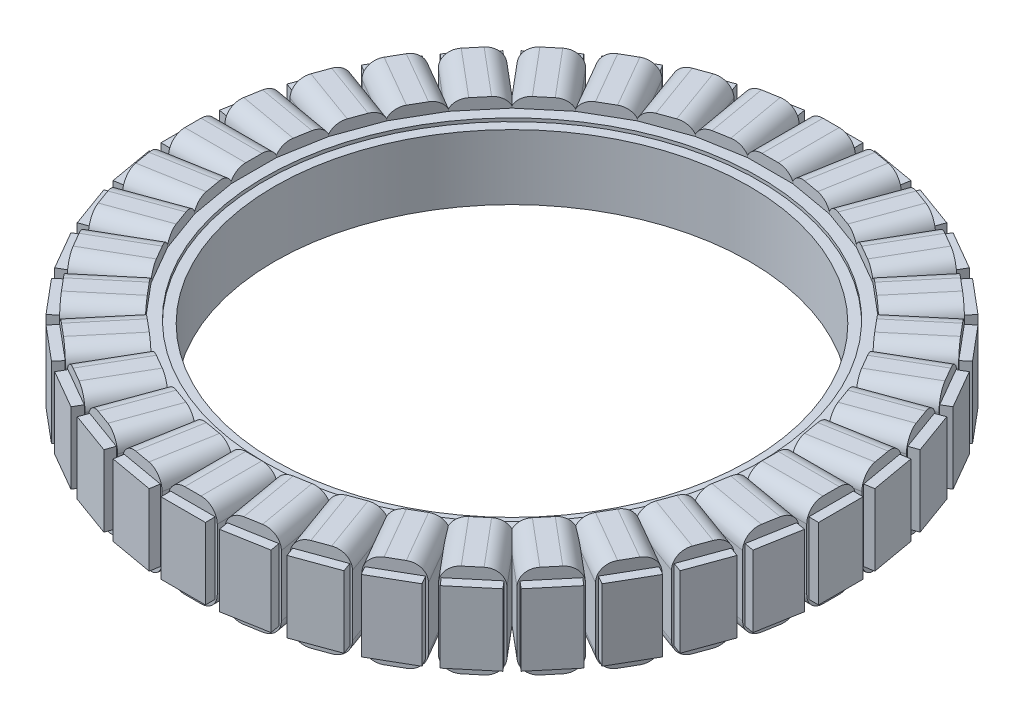
SolidWorks part; units mm, degrees
ref_plane "Front Plane" through (0, 0, 0) normal (0, 0, 1) x (1, 0, 0)
ref_plane "Top Plane" through (0, 0, 0) normal (0, 1, 0) x (1, 0, 0)
ref_plane "Right Plane" through (0, 0, 0) normal (1, 0, 0) x (0, 0, -1)
sketch "Sketch1" plane through (0, 0, 0) normal (0, 1, 0) x (1, 0, 0)
  circle A0 centre (0, 0) radius 29.25
  circle A1 centre (0, 0) radius 30.45
  dimension "D1" = 58.5
  dimension "D2" = 1.2
extrude "Boss-Extrude1" add sketch "Sketch1" along normal mid plane 8
sketch "Sketch2" plane through (0, 0, 0) normal (0, 1, 0) x (1, 0, 0)
  line L0 (0, 0) -> (0, 40.5) construction
  line L1 (-3.5433, 40.5) -> (-10.5222, 39.2694)
  line L2 (-10.5222, 39.2694) -> (-17.1814, 36.8457)
  line L3 (-17.1814, 36.8457) -> (-23.3186, 33.3024)
  line L4 (-23.3186, 33.3024) -> (-28.7472, 28.7472)
  line L5 (-28.7472, 28.7472) -> (-33.3024, 23.3186)
  line L6 (-33.3024, 23.3186) -> (-36.8457, 17.1814)
  line L7 (-36.8457, 17.1814) -> (-39.2694, 10.5222)
  line L8 (-39.2694, 10.5222) -> (-40.5, 3.5433)
  line L9 (-40.5, 3.5433) -> (-40.5, -3.5433)
  line L10 (-40.5, -3.5433) -> (-39.2694, -10.5222)
  line L11 (-39.2694, -10.5222) -> (-36.8457, -17.1814)
  line L12 (-36.8457, -17.1814) -> (-33.3024, -23.3186)
  line L13 (-33.3024, -23.3186) -> (-28.7472, -28.7472)
  line L14 (-28.7472, -28.7472) -> (-23.3186, -33.3024)
  line L15 (-23.3186, -33.3024) -> (-17.1814, -36.8457)
  line L16 (-17.1814, -36.8457) -> (-10.5222, -39.2694)
  line L17 (-10.5222, -39.2694) -> (-3.5433, -40.5)
  line L18 (-3.5433, -40.5) -> (3.5433, -40.5)
  line L19 (3.5433, -40.5) -> (10.5222, -39.2694)
  line L20 (10.5222, -39.2694) -> (17.1814, -36.8457)
  line L21 (17.1814, -36.8457) -> (23.3186, -33.3024)
  line L22 (23.3186, -33.3024) -> (28.7472, -28.7472)
  line L23 (28.7472, -28.7472) -> (33.3024, -23.3186)
  line L24 (33.3024, -23.3186) -> (36.8457, -17.1814)
  line L25 (36.8457, -17.1814) -> (39.2694, -10.5222)
  line L26 (39.2694, -10.5222) -> (40.5, -3.5433)
  line L27 (40.5, -3.5433) -> (40.5, 3.5433)
  line L28 (40.5, 3.5433) -> (39.2694, 10.5222)
  line L29 (39.2694, 10.5222) -> (36.8457, 17.1814)
  line L30 (36.8457, 17.1814) -> (33.3024, 23.3186)
  line L31 (33.3024, 23.3186) -> (28.7472, 28.7472)
  line L32 (28.7472, 28.7472) -> (23.3186, 33.3024)
  line L33 (23.3186, 33.3024) -> (17.1814, 36.8457)
  line L34 (17.1814, 36.8457) -> (10.5222, 39.2694)
  line L35 (10.5222, 39.2694) -> (3.5433, 40.5)
  line L36 (3.5433, 40.5) -> (-3.5433, 40.5)
  circle A1 centre (0, 0) radius 30.45
  circle A2 centre (0, 0) radius 40.5 construction
  circle A3 centre (0, 0) radius 30.45 construction
  dimension "D1" = 81
extrude "Boss-Extrude2" add sketch "Sketch2" along normal mid plane 8.8
sketch "Sketch4" plane through (0, 4.4, 0) normal (0, 1, 0) x (1, 0, 0)
  line L0 (0, 0) -> (0, 40.5) construction
  line L1 (3.5433, 40.5) -> (-3.5433, 40.5) construction
  line L2 (0, 0) -> (3.5433, 40.5) construction
  line L3 (1, 39.3) -> (2.7402, 39.3)
  line L4 (1, 39.3) -> (1, 31.9846)
  line L5 (10.5222, 39.2694) -> (3.5433, 40.5) construction
  line L6 (1, 31.9846) -> (4.5693, 31.6723)
  line L7 (4.5693, 31.6723) -> (5.8396, 38.8766)
  line L8 (2.7402, 39.3) -> (2.7402, 40.5)
  line L9 (2.7402, 40.5) -> (3.5433, 40.5)
  line L10 (3.5433, 40.5) -> (4.3341, 40.3606)
  line L11 (4.3341, 40.3606) -> (4.1258, 39.1788)
  line L12 (4.1258, 39.1788) -> (5.8396, 38.8766)
  line L13 (7.8092, 38.5293) -> (9.523, 38.2271)
  line L14 (7.8092, 38.5293) -> (6.5389, 31.325)
  line L15 (6.5389, 31.325) -> (9.9997, 30.3977)
  line L16 (9.9997, 30.3977) -> (12.5017, 37.2719)
  line L17 (9.523, 38.2271) -> (9.7314, 39.4089)
  line L18 (9.7314, 39.4089) -> (10.5222, 39.2694)
  line L19 (10.5222, 39.2694) -> (11.2768, 38.9948)
  line L20 (11.2768, 38.9948) -> (10.8664, 37.8671)
  line L21 (10.8664, 37.8671) -> (12.5017, 37.2719)
  line L22 (14.3811, 36.5879) -> (16.0164, 35.9927)
  line L23 (14.3811, 36.5879) -> (11.8791, 29.7136)
  line L24 (11.8791, 29.7136) -> (15.1263, 28.1994)
  line L25 (15.1263, 28.1994) -> (18.784, 34.5348)
  line L26 (16.0164, 35.9927) -> (16.4268, 37.1203)
  line L27 (16.4268, 37.1203) -> (17.1814, 36.8457)
  line L28 (17.1814, 36.8457) -> (17.8769, 36.4441)
  line L29 (17.8769, 36.4441) -> (17.2769, 35.4049)
  line L30 (17.2769, 35.4049) -> (18.784, 34.5348)
  line L31 (20.516, 33.5348) -> (22.0231, 32.6647)
  line L32 (20.516, 33.5348) -> (16.8583, 27.1994)
  line L33 (16.8583, 27.1994) -> (19.7932, 25.1444)
  line L34 (19.7932, 25.1444) -> (24.4955, 30.7483)
  line L35 (22.0231, 32.6647) -> (22.6231, 33.7039)
  line L36 (22.6231, 33.7039) -> (23.3186, 33.3024)
  line L37 (23.3186, 33.3024) -> (23.9338, 32.7862)
  line L38 (23.9338, 32.7862) -> (23.1624, 31.8669)
  line L39 (23.1624, 31.8669) -> (24.4955, 30.7483)
  line L40 (26.0276, 29.4628) -> (27.3607, 28.3442)
  line L41 (26.0276, 29.4628) -> (21.3253, 23.8588)
  line L42 (21.3253, 23.8588) -> (23.8588, 21.3253)
  line L43 (23.8588, 21.3253) -> (29.4628, 26.0276)
  line L44 (27.3607, 28.3442) -> (28.132, 29.2634)
  line L45 (28.132, 29.2634) -> (28.7472, 28.7472)
  line L46 (28.7472, 28.7472) -> (29.2634, 28.132)
  line L47 (29.2634, 28.132) -> (28.3442, 27.3607)
  line L48 (28.3442, 27.3607) -> (29.4628, 26.0276)
  line L49 (30.7483, 24.4955) -> (31.8669, 23.1624)
  line L50 (30.7483, 24.4955) -> (25.1444, 19.7932)
  line L51 (25.1444, 19.7932) -> (27.1994, 16.8583)
  line L52 (27.1994, 16.8583) -> (33.5348, 20.516)
  line L53 (31.8669, 23.1624) -> (32.7862, 23.9338)
  line L54 (32.7862, 23.9338) -> (33.3024, 23.3186)
  line L55 (33.3024, 23.3186) -> (33.7039, 22.6231)
  line L56 (33.7039, 22.6231) -> (32.6647, 22.0231)
  line L57 (32.6647, 22.0231) -> (33.5348, 20.516)
  line L58 (34.5348, 18.784) -> (35.4049, 17.2769)
  line L59 (34.5348, 18.784) -> (28.1994, 15.1263)
  line L60 (28.1994, 15.1263) -> (29.7136, 11.8791)
  line L61 (29.7136, 11.8791) -> (36.5879, 14.3811)
  line L62 (35.4049, 17.2769) -> (36.4441, 17.8769)
  line L63 (36.4441, 17.8769) -> (36.8457, 17.1814)
  line L64 (36.8457, 17.1814) -> (37.1203, 16.4268)
  line L65 (37.1203, 16.4268) -> (35.9927, 16.0164)
  line L66 (35.9927, 16.0164) -> (36.5879, 14.3811)
  line L67 (37.2719, 12.5017) -> (37.8671, 10.8664)
  line L68 (37.2719, 12.5017) -> (30.3977, 9.9997)
  line L69 (30.3977, 9.9997) -> (31.325, 6.5389)
  line L70 (31.325, 6.5389) -> (38.5293, 7.8092)
  line L71 (37.8671, 10.8664) -> (38.9948, 11.2768)
  line L72 (38.9948, 11.2768) -> (39.2694, 10.5222)
  line L73 (39.2694, 10.5222) -> (39.4089, 9.7314)
  line L74 (39.4089, 9.7314) -> (38.2271, 9.523)
  line L75 (38.2271, 9.523) -> (38.5293, 7.8092)
  line L76 (38.8766, 5.8396) -> (39.1788, 4.1258)
  line L77 (38.8766, 5.8396) -> (31.6723, 4.5693)
  line L78 (31.6723, 4.5693) -> (31.9846, 1)
  line L79 (31.9846, 1) -> (39.3, 1)
  line L80 (39.1788, 4.1258) -> (40.3606, 4.3341)
  line L81 (40.3606, 4.3341) -> (40.5, 3.5433)
  line L82 (40.5, 3.5433) -> (40.5, 2.7402)
  line L83 (40.5, 2.7402) -> (39.3, 2.7402)
  line L84 (39.3, 2.7402) -> (39.3, 1)
  line L85 (39.3, -1) -> (39.3, -2.7402)
  line L86 (39.3, -1) -> (31.9846, -1)
  line L87 (31.9846, -1) -> (31.6723, -4.5693)
  line L88 (31.6723, -4.5693) -> (38.8766, -5.8396)
  line L89 (39.3, -2.7402) -> (40.5, -2.7402)
  line L90 (40.5, -2.7402) -> (40.5, -3.5433)
  line L91 (40.5, -3.5433) -> (40.3606, -4.3341)
  line L92 (40.3606, -4.3341) -> (39.1788, -4.1258)
  line L93 (39.1788, -4.1258) -> (38.8766, -5.8396)
  line L94 (38.5293, -7.8092) -> (38.2271, -9.523)
  line L95 (38.5293, -7.8092) -> (31.325, -6.5389)
  line L96 (31.325, -6.5389) -> (30.3977, -9.9997)
  line L97 (30.3977, -9.9997) -> (37.2719, -12.5017)
  line L98 (38.2271, -9.523) -> (39.4089, -9.7314)
  line L99 (39.4089, -9.7314) -> (39.2694, -10.5222)
  line L100 (39.2694, -10.5222) -> (38.9948, -11.2768)
  line L101 (38.9948, -11.2768) -> (37.8671, -10.8664)
  line L102 (37.8671, -10.8664) -> (37.2719, -12.5017)
  line L103 (36.5879, -14.3811) -> (35.9927, -16.0164)
  line L104 (36.5879, -14.3811) -> (29.7136, -11.8791)
  line L105 (29.7136, -11.8791) -> (28.1994, -15.1263)
  line L106 (28.1994, -15.1263) -> (34.5348, -18.784)
  line L107 (35.9927, -16.0164) -> (37.1203, -16.4268)
  line L108 (37.1203, -16.4268) -> (36.8457, -17.1814)
  line L109 (36.8457, -17.1814) -> (36.4441, -17.8769)
  line L110 (36.4441, -17.8769) -> (35.4049, -17.2769)
  line L111 (35.4049, -17.2769) -> (34.5348, -18.784)
  line L112 (33.5348, -20.516) -> (32.6647, -22.0231)
  line L113 (33.5348, -20.516) -> (27.1994, -16.8583)
  line L114 (27.1994, -16.8583) -> (25.1444, -19.7932)
  line L115 (25.1444, -19.7932) -> (30.7483, -24.4955)
  line L116 (32.6647, -22.0231) -> (33.7039, -22.6231)
  line L117 (33.7039, -22.6231) -> (33.3024, -23.3186)
  line L118 (33.3024, -23.3186) -> (32.7862, -23.9338)
  line L119 (32.7862, -23.9338) -> (31.8669, -23.1624)
  line L120 (31.8669, -23.1624) -> (30.7483, -24.4955)
  line L121 (29.4628, -26.0276) -> (28.3442, -27.3607)
  line L122 (29.4628, -26.0276) -> (23.8588, -21.3253)
  line L123 (23.8588, -21.3253) -> (21.3253, -23.8588)
  line L124 (21.3253, -23.8588) -> (26.0276, -29.4628)
  line L125 (28.3442, -27.3607) -> (29.2634, -28.132)
  line L126 (29.2634, -28.132) -> (28.7472, -28.7472)
  line L127 (28.7472, -28.7472) -> (28.132, -29.2634)
  line L128 (28.132, -29.2634) -> (27.3607, -28.3442)
  line L129 (27.3607, -28.3442) -> (26.0276, -29.4628)
  line L130 (24.4955, -30.7483) -> (23.1624, -31.8669)
  line L131 (24.4955, -30.7483) -> (19.7932, -25.1444)
  line L132 (19.7932, -25.1444) -> (16.8583, -27.1994)
  line L133 (16.8583, -27.1994) -> (20.516, -33.5348)
  line L134 (23.1624, -31.8669) -> (23.9338, -32.7862)
  line L135 (23.9338, -32.7862) -> (23.3186, -33.3024)
  line L136 (23.3186, -33.3024) -> (22.6231, -33.7039)
  line L137 (22.6231, -33.7039) -> (22.0231, -32.6647)
  line L138 (22.0231, -32.6647) -> (20.516, -33.5348)
  line L139 (18.784, -34.5348) -> (17.2769, -35.4049)
  line L140 (18.784, -34.5348) -> (15.1263, -28.1994)
  line L141 (15.1263, -28.1994) -> (11.8791, -29.7136)
  line L142 (11.8791, -29.7136) -> (14.3811, -36.5879)
  line L143 (17.2769, -35.4049) -> (17.8769, -36.4441)
  line L144 (17.8769, -36.4441) -> (17.1814, -36.8457)
  line L145 (17.1814, -36.8457) -> (16.4268, -37.1203)
  line L146 (16.4268, -37.1203) -> (16.0164, -35.9927)
  line L147 (16.0164, -35.9927) -> (14.3811, -36.5879)
  line L148 (12.5017, -37.2719) -> (10.8664, -37.8671)
  line L149 (12.5017, -37.2719) -> (9.9997, -30.3977)
  line L150 (9.9997, -30.3977) -> (6.5389, -31.325)
  line L151 (6.5389, -31.325) -> (7.8092, -38.5293)
  line L152 (10.8664, -37.8671) -> (11.2768, -38.9948)
  line L153 (11.2768, -38.9948) -> (10.5222, -39.2694)
  line L154 (10.5222, -39.2694) -> (9.7314, -39.4089)
  line L155 (9.7314, -39.4089) -> (9.523, -38.2271)
  line L156 (9.523, -38.2271) -> (7.8092, -38.5293)
  line L157 (5.8396, -38.8766) -> (4.1258, -39.1788)
  line L158 (5.8396, -38.8766) -> (4.5693, -31.6723)
  line L159 (4.5693, -31.6723) -> (1, -31.9846)
  line L160 (1, -31.9846) -> (1, -39.3)
  line L161 (4.1258, -39.1788) -> (4.3341, -40.3606)
  line L162 (4.3341, -40.3606) -> (3.5433, -40.5)
  line L163 (3.5433, -40.5) -> (2.7402, -40.5)
  line L164 (2.7402, -40.5) -> (2.7402, -39.3)
  line L165 (2.7402, -39.3) -> (1, -39.3)
  line L166 (-1, -39.3) -> (-2.7402, -39.3)
  line L167 (-1, -39.3) -> (-1, -31.9846)
  line L168 (-1, -31.9846) -> (-4.5693, -31.6723)
  line L169 (-4.5693, -31.6723) -> (-5.8396, -38.8766)
  line L170 (-2.7402, -39.3) -> (-2.7402, -40.5)
  line L171 (-2.7402, -40.5) -> (-3.5433, -40.5)
  line L172 (-3.5433, -40.5) -> (-4.3341, -40.3606)
  line L173 (-4.3341, -40.3606) -> (-4.1258, -39.1788)
  line L174 (-4.1258, -39.1788) -> (-5.8396, -38.8766)
  line L175 (-7.8092, -38.5293) -> (-9.523, -38.2271)
  line L176 (-7.8092, -38.5293) -> (-6.5389, -31.325)
  line L177 (-6.5389, -31.325) -> (-9.9997, -30.3977)
  line L178 (-9.9997, -30.3977) -> (-12.5017, -37.2719)
  line L179 (-9.523, -38.2271) -> (-9.7314, -39.4089)
  line L180 (-9.7314, -39.4089) -> (-10.5222, -39.2694)
  line L181 (-10.5222, -39.2694) -> (-11.2768, -38.9948)
  line L182 (-11.2768, -38.9948) -> (-10.8664, -37.8671)
  line L183 (-10.8664, -37.8671) -> (-12.5017, -37.2719)
  line L184 (-14.3811, -36.5879) -> (-16.0164, -35.9927)
  line L185 (-14.3811, -36.5879) -> (-11.8791, -29.7136)
  line L186 (-11.8791, -29.7136) -> (-15.1263, -28.1994)
  line L187 (-15.1263, -28.1994) -> (-18.784, -34.5348)
  line L188 (-16.0164, -35.9927) -> (-16.4268, -37.1203)
  line L189 (-16.4268, -37.1203) -> (-17.1814, -36.8457)
  line L190 (-17.1814, -36.8457) -> (-17.8769, -36.4441)
  line L191 (-17.8769, -36.4441) -> (-17.2769, -35.4049)
  line L192 (-17.2769, -35.4049) -> (-18.784, -34.5348)
  line L193 (-20.516, -33.5348) -> (-22.0231, -32.6647)
  line L194 (-20.516, -33.5348) -> (-16.8583, -27.1994)
  line L195 (-16.8583, -27.1994) -> (-19.7932, -25.1444)
  line L196 (-19.7932, -25.1444) -> (-24.4955, -30.7483)
  line L197 (-22.0231, -32.6647) -> (-22.6231, -33.7039)
  line L198 (-22.6231, -33.7039) -> (-23.3186, -33.3024)
  line L199 (-23.3186, -33.3024) -> (-23.9338, -32.7862)
  line L200 (-23.9338, -32.7862) -> (-23.1624, -31.8669)
  line L201 (-23.1624, -31.8669) -> (-24.4955, -30.7483)
  line L202 (-26.0276, -29.4628) -> (-27.3607, -28.3442)
  line L203 (-26.0276, -29.4628) -> (-21.3253, -23.8588)
  line L204 (-21.3253, -23.8588) -> (-23.8588, -21.3253)
  line L205 (-23.8588, -21.3253) -> (-29.4628, -26.0276)
  line L206 (-27.3607, -28.3442) -> (-28.132, -29.2634)
  line L207 (-28.132, -29.2634) -> (-28.7472, -28.7472)
  line L208 (-28.7472, -28.7472) -> (-29.2634, -28.132)
  line L209 (-29.2634, -28.132) -> (-28.3442, -27.3607)
  line L210 (-28.3442, -27.3607) -> (-29.4628, -26.0276)
  line L211 (-30.7483, -24.4955) -> (-31.8669, -23.1624)
  line L212 (-30.7483, -24.4955) -> (-25.1444, -19.7932)
  line L213 (-25.1444, -19.7932) -> (-27.1994, -16.8583)
  line L214 (-27.1994, -16.8583) -> (-33.5348, -20.516)
  line L215 (-31.8669, -23.1624) -> (-32.7862, -23.9338)
  line L216 (-32.7862, -23.9338) -> (-33.3024, -23.3186)
  line L217 (-33.3024, -23.3186) -> (-33.7039, -22.6231)
  line L218 (-33.7039, -22.6231) -> (-32.6647, -22.0231)
  line L219 (-32.6647, -22.0231) -> (-33.5348, -20.516)
  line L220 (-34.5348, -18.784) -> (-35.4049, -17.2769)
  line L221 (-34.5348, -18.784) -> (-28.1994, -15.1263)
  line L222 (-28.1994, -15.1263) -> (-29.7136, -11.8791)
  line L223 (-29.7136, -11.8791) -> (-36.5879, -14.3811)
  line L224 (-35.4049, -17.2769) -> (-36.4441, -17.8769)
  line L225 (-36.4441, -17.8769) -> (-36.8457, -17.1814)
  line L226 (-36.8457, -17.1814) -> (-37.1203, -16.4268)
  line L227 (-37.1203, -16.4268) -> (-35.9927, -16.0164)
  line L228 (-35.9927, -16.0164) -> (-36.5879, -14.3811)
  line L229 (-37.2719, -12.5017) -> (-37.8671, -10.8664)
  line L230 (-37.2719, -12.5017) -> (-30.3977, -9.9997)
  line L231 (-30.3977, -9.9997) -> (-31.325, -6.5389)
  line L232 (-31.325, -6.5389) -> (-38.5293, -7.8092)
  line L233 (-37.8671, -10.8664) -> (-38.9948, -11.2768)
  line L234 (-38.9948, -11.2768) -> (-39.2694, -10.5222)
  line L235 (-39.2694, -10.5222) -> (-39.4089, -9.7314)
  line L236 (-39.4089, -9.7314) -> (-38.2271, -9.523)
  line L237 (-38.2271, -9.523) -> (-38.5293, -7.8092)
  line L238 (-38.8766, -5.8396) -> (-39.1788, -4.1258)
  line L239 (-38.8766, -5.8396) -> (-31.6723, -4.5693)
  line L240 (-31.6723, -4.5693) -> (-31.9846, -1)
  line L241 (-31.9846, -1) -> (-39.3, -1)
  line L242 (-39.1788, -4.1258) -> (-40.3606, -4.3341)
  line L243 (-40.3606, -4.3341) -> (-40.5, -3.5433)
  line L244 (-40.5, -3.5433) -> (-40.5, -2.7402)
  line L245 (-40.5, -2.7402) -> (-39.3, -2.7402)
  line L246 (-39.3, -2.7402) -> (-39.3, -1)
  line L247 (-39.3, 1) -> (-39.3, 2.7402)
  line L248 (-39.3, 1) -> (-31.9846, 1)
  line L249 (-31.9846, 1) -> (-31.6723, 4.5693)
  line L250 (-31.6723, 4.5693) -> (-38.8766, 5.8396)
  line L251 (-39.3, 2.7402) -> (-40.5, 2.7402)
  line L252 (-40.5, 2.7402) -> (-40.5, 3.5433)
  line L253 (-40.5, 3.5433) -> (-40.3606, 4.3341)
  line L254 (-40.3606, 4.3341) -> (-39.1788, 4.1258)
  line L255 (-39.1788, 4.1258) -> (-38.8766, 5.8396)
  line L256 (-38.5293, 7.8092) -> (-38.2271, 9.523)
  line L257 (-38.5293, 7.8092) -> (-31.325, 6.5389)
  line L258 (-31.325, 6.5389) -> (-30.3977, 9.9997)
  line L259 (-30.3977, 9.9997) -> (-37.2719, 12.5017)
  line L260 (-38.2271, 9.523) -> (-39.4089, 9.7314)
  line L261 (-39.4089, 9.7314) -> (-39.2694, 10.5222)
  line L262 (-39.2694, 10.5222) -> (-38.9948, 11.2768)
  line L263 (-38.9948, 11.2768) -> (-37.8671, 10.8664)
  line L264 (-37.8671, 10.8664) -> (-37.2719, 12.5017)
  line L265 (-36.5879, 14.3811) -> (-35.9927, 16.0164)
  line L266 (-36.5879, 14.3811) -> (-29.7136, 11.8791)
  line L267 (-29.7136, 11.8791) -> (-28.1994, 15.1263)
  line L268 (-28.1994, 15.1263) -> (-34.5348, 18.784)
  line L269 (-35.9927, 16.0164) -> (-37.1203, 16.4268)
  line L270 (-37.1203, 16.4268) -> (-36.8457, 17.1814)
  line L271 (-36.8457, 17.1814) -> (-36.4441, 17.8769)
  line L272 (-36.4441, 17.8769) -> (-35.4049, 17.2769)
  line L273 (-35.4049, 17.2769) -> (-34.5348, 18.784)
  line L274 (-33.5348, 20.516) -> (-32.6647, 22.0231)
  line L275 (-33.5348, 20.516) -> (-27.1994, 16.8583)
  line L276 (-27.1994, 16.8583) -> (-25.1444, 19.7932)
  line L277 (-25.1444, 19.7932) -> (-30.7483, 24.4955)
  line L278 (-32.6647, 22.0231) -> (-33.7039, 22.6231)
  line L279 (-33.7039, 22.6231) -> (-33.3024, 23.3186)
  line L280 (-33.3024, 23.3186) -> (-32.7862, 23.9338)
  line L281 (-32.7862, 23.9338) -> (-31.8669, 23.1624)
  line L282 (-31.8669, 23.1624) -> (-30.7483, 24.4955)
  line L283 (-29.4628, 26.0276) -> (-28.3442, 27.3607)
  line L284 (-29.4628, 26.0276) -> (-23.8588, 21.3253)
  line L285 (-23.8588, 21.3253) -> (-21.3253, 23.8588)
  line L286 (-21.3253, 23.8588) -> (-26.0276, 29.4628)
  line L287 (-28.3442, 27.3607) -> (-29.2634, 28.132)
  line L288 (-29.2634, 28.132) -> (-28.7472, 28.7472)
  line L289 (-28.7472, 28.7472) -> (-28.132, 29.2634)
  line L290 (-28.132, 29.2634) -> (-27.3607, 28.3442)
  line L291 (-27.3607, 28.3442) -> (-26.0276, 29.4628)
  line L292 (-24.4955, 30.7483) -> (-23.1624, 31.8669)
  line L293 (-24.4955, 30.7483) -> (-19.7932, 25.1444)
  line L294 (-19.7932, 25.1444) -> (-16.8583, 27.1994)
  line L295 (-16.8583, 27.1994) -> (-20.516, 33.5348)
  line L296 (-23.1624, 31.8669) -> (-23.9338, 32.7862)
  line L297 (-23.9338, 32.7862) -> (-23.3186, 33.3024)
  line L298 (-23.3186, 33.3024) -> (-22.6231, 33.7039)
  line L299 (-22.6231, 33.7039) -> (-22.0231, 32.6647)
  line L300 (-22.0231, 32.6647) -> (-20.516, 33.5348)
  line L301 (-18.784, 34.5348) -> (-17.2769, 35.4049)
  line L302 (-18.784, 34.5348) -> (-15.1263, 28.1994)
  line L303 (-15.1263, 28.1994) -> (-11.8791, 29.7136)
  line L304 (-11.8791, 29.7136) -> (-14.3811, 36.5879)
  line L305 (-17.2769, 35.4049) -> (-17.8769, 36.4441)
  line L306 (-17.8769, 36.4441) -> (-17.1814, 36.8457)
  line L307 (-17.1814, 36.8457) -> (-16.4268, 37.1203)
  line L308 (-16.4268, 37.1203) -> (-16.0164, 35.9927)
  line L309 (-16.0164, 35.9927) -> (-14.3811, 36.5879)
  line L310 (-12.5017, 37.2719) -> (-10.8664, 37.8671)
  line L311 (-12.5017, 37.2719) -> (-9.9997, 30.3977)
  line L312 (-9.9997, 30.3977) -> (-6.5389, 31.325)
  line L313 (-6.5389, 31.325) -> (-7.8092, 38.5293)
  line L314 (-10.8664, 37.8671) -> (-11.2768, 38.9948)
  line L315 (-11.2768, 38.9948) -> (-10.5222, 39.2694)
  line L316 (-10.5222, 39.2694) -> (-9.7314, 39.4089)
  line L317 (-9.7314, 39.4089) -> (-9.523, 38.2271)
  line L318 (-9.523, 38.2271) -> (-7.8092, 38.5293)
  line L319 (-5.8396, 38.8766) -> (-4.1258, 39.1788)
  line L320 (-5.8396, 38.8766) -> (-4.5693, 31.6723)
  line L321 (-4.5693, 31.6723) -> (-1, 31.9846)
  line L322 (-1, 31.9846) -> (-1, 39.3)
  line L323 (-4.1258, 39.1788) -> (-4.3341, 40.3606)
  line L324 (-4.3341, 40.3606) -> (-3.5433, 40.5)
  line L325 (-3.5433, 40.5) -> (-2.7402, 40.5)
  line L326 (-2.7402, 40.5) -> (-2.7402, 39.3)
  line L327 (-2.7402, 39.3) -> (-1, 39.3)
  circle A0 centre (0, 0) radius 30.45 construction
  point P337 (0, 0)
  dimension "D1" = 31.95
  dimension "D2" = 1.2
  dimension "D3" = 1
  dimension "D4" = 1.6
  dimension "D5" = 36
extrude "Cut-Extrude1" cut sketch "Sketch4" against normal up to surface (8.8 mm away) up to face at (0, -4.4, 0)
sketch "Sketch5" plane through (0, 0, -39.3) normal (0, 0, 1) x (1, 0, 0)
  line L0 (1, 5.75) -> (-1, 5.75)
  line L1 (-3, -5.75) -> (3, -5.75) construction
  line L2 (-3, -5.75) -> (-3, 5.75) construction
  line L3 (-3, 5.75) -> (3, 5.75) construction
  line L4 (3, -5.75) -> (3, 5.75) construction
  line L5 (-3, -5.75) -> (3, 5.75) construction
  line L6 (-3, 5.75) -> (3, -5.75) construction
  line L7 (-3, 3.75) -> (-3, -3.75)
  line L8 (3, 3.75) -> (3, -3.75)
  line L9 (1, -5.75) -> (-1, -5.75)
  arc A0 (-1, -5.75) -> (-3, -3.75) centre (-1, -3.75) cw
  arc A1 (1, -5.75) -> (3, -3.75) centre (1, -3.75) ccw
  arc A2 (3, 3.75) -> (1, 5.75) centre (1, 3.75) ccw
  arc A3 (-1, 5.75) -> (-3, 3.75) centre (-1, 3.75) ccw
  point P0 (0, 0)
  dimension "D3" = 2
  dimension "D1" = 11.5
  dimension "D2" = 6
extrude "Boss-Extrude3" add sketch "Sketch5" along normal blind 7.5
pattern_circular "CirPattern1" count 36 over 360 about axis through (0, 0, 0) along (0, 1, 0) of "Boss-Extrude3"
